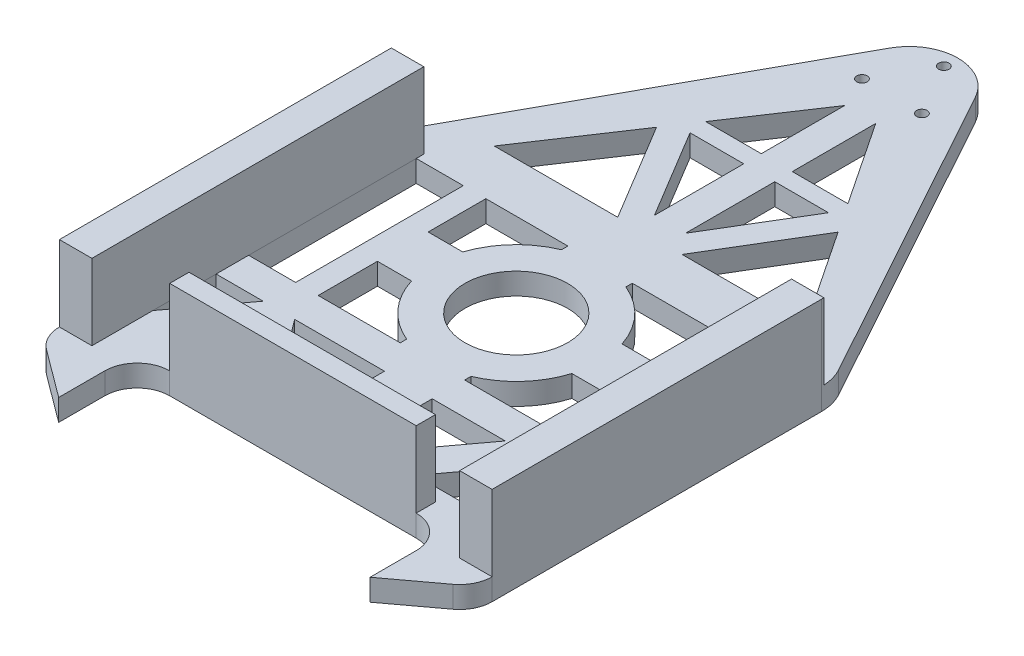
SolidWorks part; units mm, degrees
material "Cast Stainless Steel"
ref_plane "Front Plane" through (0, 0, 0) normal (0, 0, 1) x (1, 0, 0)
ref_plane "Top Plane" through (0, 0, 0) normal (0, 1, 0) x (1, 0, 0)
ref_plane "Right Plane" through (0, 0, 0) normal (1, 0, 0) x (0, 0, -1)
sketch "Sketch1" plane through (0, 0, 0) normal (0, 1, 0) x (1, 0, 0)
  line L0 (-324.5, 0) -> (-36.6111, 0)
  line L1 (19.4444, 0) -> (19.4444, 300)
  line L2 (-150.7834, 18.3812) -> (-143.0581, 18.3812)
  line L3 (-150.7834, 98.9559) -> (-83.2032, 98.9559)
  line L4 (-380.5556, 300) -> (-380.5556, 0)
  line L5 (-380.5556, 0) -> (-380.5556, -30.9894)
  line L6 (19.4444, 300) -> (25, 294.4444)
  line L7 (-350.5556, 98.9559) -> (-307.0461, 98.9559)
  line L8 (-350.5556, 40.385) -> (-307.0461, 98.9559)
  line L9 (-218.053, 18.3812) -> (-277.9079, 98.9559)
  line L10 (-143.0581, 18.3812) -> (-83.2032, 98.9559)
  line L11 (-40.2128, 30) -> (-97.0554, 30)
  line L12 (-350.5556, 128.9559) -> (-307.0461, 128.9559)
  line L13 (-194.896, 524.4061) -> (-246.3088, 447.2869)
  line L14 (-36.6111, 330) -> (-96.6333, 420.0334)
  line L15 (-324.5, 330) -> (-210.3278, 330)
  line L16 (-10.5556, 40.385) -> (-54.065, 98.9559)
  line L17 (-194.896, 18.3812) -> (-194.896, 98.9559)
  line L19 (-350.5556, 283.9559) -> (-307.0461, 283.9559)
  line L20 (-350.5556, 283.9559) -> (-350.5556, 221.4578)
  line L21 (-10.5556, 128.9559) -> (-10.5556, 178.791)
  line L22 (-350.5556, 300) -> (-350.5556, 0) construction
  line L23 (-380.5556, -30.9894) -> (-324.5, -72.6302)
  line L24 (-380.5556, 128.9559) -> (19.4444, 128.9559) construction
  line L25 (-292.477, 115.7535) -> (-292.477, 91.7007) construction
  line L26 (-97.0554, 30) -> (-68.6341, 68.2598)
  line L27 (-218.053, 18.3812) -> (-194.896, 18.3812)
  line L28 (-40.2128, 30) -> (-68.6341, 68.2598)
  line L29 (-320.8984, 30) -> (-264.0557, 30)
  line L30 (-150.7834, 330) -> (-36.6111, 330)
  line L31 (-320.8984, 30) -> (-292.477, 68.2598)
  line L32 (-54.065, 98.9559) -> (-10.5556, 98.9559)
  line L33 (-277.9079, 98.9559) -> (-194.896, 98.9559)
  line L34 (-264.0557, 30) -> (-292.477, 68.2598)
  line L35 (-380.5556, 98.9559) -> (19.4444, 98.9559) construction
  line L36 (-324.5, -72.6302) -> (-324.5, 0)
  line L37 (-36.6111, -72.6302) -> (-36.6111, 0)
  line L38 (-246.3088, 447.2869) -> (-194.896, 447.2869)
  line L39 (-180.5556, 424.8555) -> (-180.5556, 662.9762) construction
  line L40 (-380.5556, 300) -> (-180.5556, 662.9762)
  line L41 (-180.5556, 424.8555) -> (-180.5556, 353.486) construction
  line L42 (-180.5556, 662.9762) -> (19.4444, 300)
  line L43 (-150.7834, 18.3812) -> (-150.7834, 98.9559)
  line L44 (-307.0461, 283.9559) -> (-307.0461, 221.4578)
  line L45 (-286.1825, 283.9559) -> (-286.1825, 230.6106)
  line L46 (-548.4441, 206.4559) -> (-478.3267, 206.4559) construction
  line L47 (-307.0461, 128.9559) -> (-307.0461, 178.791)
  line L48 (-286.1825, 128.9559) -> (-286.1825, 183.7221)
  line L49 (19.4444, -30.9894) -> (-36.6111, -72.6302)
  line L50 (19.4444, 0) -> (19.4444, -30.9894)
  line L51 (-380.5556, 0) -> (-380.5556, -30.9894)
  line L52 (19.4444, 0) -> (19.4444, -30.9894)
  line L53 (-350.5556, 98.9559) -> (-350.5556, 40.385)
  line L54 (-10.5556, 98.9559) -> (-10.5556, 40.385)
  line L55 (-210.3278, 134.9027) -> (-210.3278, 128.9559)
  line L56 (-150.7834, 134.9027) -> (-150.7834, 128.9559)
  line L57 (-210.3278, 278.0092) -> (-210.3278, 283.9559)
  line L58 (-150.7834, 278.0092) -> (-150.7834, 283.9559)
  line L59 (-74.9286, 128.9559) -> (-74.9286, 183.7221)
  line L60 (-54.065, 128.9559) -> (-54.065, 178.791)
  line L61 (-74.9286, 283.9559) -> (-74.9286, 230.6106)
  line L62 (-54.065, 283.9559) -> (-54.065, 221.4578)
  line L63 (-350.5556, 178.791) -> (-350.5556, 128.9559)
  line L64 (-116.5717, 431.0826) -> (-166.2152, 431.0826)
  line L65 (-114.8023, 447.2869) -> (-166.2152, 524.4061)
  line L66 (-194.896, 524.4061) -> (-194.896, 447.2869)
  line L67 (-166.2152, 524.4061) -> (-166.2152, 447.2869)
  line L68 (-244.5394, 431.0826) -> (-194.896, 348.542)
  line L69 (-264.4778, 420.0334) -> (-210.3278, 330)
  line L70 (-116.5717, 431.0826) -> (-166.2152, 348.542)
  line L71 (-96.6333, 420.0334) -> (-150.7834, 330)
  line L72 (-166.2152, 447.2869) -> (-114.8023, 447.2869)
  line L73 (-194.896, 431.0826) -> (-244.5394, 431.0826)
  line L74 (-194.896, 431.0826) -> (-194.896, 348.542)
  line L75 (-166.2152, 431.0826) -> (-166.2152, 348.542)
  line L76 (-264.4778, 420.0334) -> (-324.5, 330)
  line L77 (-10.5556, 221.4578) -> (-10.5556, 283.9559)
  line L78 (-74.9286, 183.7221) -> (-106.4649, 183.7221)
  line L79 (-74.9286, 230.6106) -> (-106.9159, 230.6106)
  line L80 (-286.1825, 183.7221) -> (-254.6462, 183.7221)
  line L81 (-286.1825, 230.6106) -> (-254.1952, 230.6106)
  line L82 (-286.1825, 283.9559) -> (-210.3278, 283.9559)
  line L83 (-286.1825, 128.9559) -> (-210.3278, 128.9559)
  line L84 (-54.065, 128.9559) -> (-10.5556, 128.9559)
  line L85 (-54.065, 283.9559) -> (-10.5556, 283.9559)
  line L86 (-150.7834, 283.9559) -> (-74.9286, 283.9559)
  line L87 (-150.7834, 128.9559) -> (-74.9286, 128.9559)
  line L88 (-10.5556, 221.4578) -> (-10.5556, 178.791)
  line L89 (-54.065, 221.4578) -> (-54.065, 178.791)
  line L90 (-307.0461, 221.4578) -> (-307.0461, 178.791)
  line L91 (-350.5556, 221.4578) -> (-350.5556, 178.791)
  arc A0 (-254.6462, 183.7221) -> (-210.3278, 134.9027) centre (-180.5556, 206.4559) ccw
  circle A1 centre (-180.5556, 206.4559) radius 47.5
  arc A2 (-106.9159, 230.6106) -> (-150.7834, 278.0092) centre (-180.5556, 206.4559) ccw
  circle A3 centre (-180.5556, 206.4559) radius 77.5 construction
  arc A4 (-210.3278, 278.0092) -> (-254.1952, 230.6106) centre (-180.5556, 206.4559) ccw
  arc A5 (-150.7834, 134.9027) -> (-106.4649, 183.7221) centre (-180.5556, 206.4559) ccw
  point P3 (-180.5556, 0)
  point P11 (-279.5115, 98.9559)
  point P12 (-5.5171, 283.359)
  point P13 (-81.5996, 98.9559)
  point P14 (-180.5556, 545.9167)
  point P15 (-355.594, 283.359)
  point P16 (-380.5556, 330)
  point P17 (19.4444, 330)
  point P23 (-10.5556, 0)
  point P24 (-10.5556, 300)
  point P25 (-380.5556, 270)
  point P26 (19.4444, 270)
  point P33 (-81.3793, 56.7498)
  point P34 (-1.5461, -21.4335)
  point P35 (-180.5556, -42.4264)
  point P36 (-279.7318, 56.7498)
  point P37 (-359.565, -21.4335)
  point P38 (-380.5556, 30)
  point P39 (19.4444, 30)
  point P69 (-307.0461, 153.8735)
  point P74 (-356.4732, -17.8896)
  point P83 (-54.065, 153.8735)
  point P93 (-113.115, 220.0966)
  point P112 (-282.9637, 81.0663)
  point P113 (-228.4809, -17.8896)
  point P114 (-301.9903, 81.0663)
  point P115 (-380.5556, 30)
  point P126 (-328.8008, 128.9559)
  dimension "D1" = 155
  dimension "D3" = 400
  dimension "D8" = 53.393
  dimension "D5" = 30
  dimension "D7" = 30
  dimension "D9" = 30
extrude "Boss-Extrude6" add sketch "Sketch1" along normal blind 20
fillet "Fillet2" radius 30 4 edges at (-324.5, 10, 0) (-36.6111, 10, 0) (19.4444, 10, 30.9894) (-380.5556, 10, 30.9894)
sketch "Sketch3" plane through (0, 20, 0) normal (0, 1, 0) x (1, 0, 0)
  line L0 (-294.5, 0) -> (-66.6111, 0)
  line L1 (-294.5, 0) -> (-294.5, 17.8282)
  line L2 (-66.6111, 0) -> (-66.6111, 17.8282)
  line L3 (-294.5, 17.8282) -> (-66.6111, 17.8282)
  line L4 (-380.5556, -15.9032) -> (-380.5556, 290.9167)
  line L5 (-380.5556, -15.9032) -> (-350.5259, -15.9032)
  line L6 (-380.5556, 290.9167) -> (-350.5259, 290.9167)
  line L7 (-350.5259, -15.9032) -> (-350.5259, 290.9167)
  line L8 (19.4444, -15.9032) -> (19.4444, 290.9167)
  line L9 (19.4444, -15.9032) -> (-10.5556, -15.9032)
  line L10 (19.4444, 290.9167) -> (-10.5556, 290.9167)
  line L11 (-10.5556, -15.9032) -> (-10.5556, 290.9167)
extrude "Boss-Extrude12" add sketch "Sketch3" along normal blind 70
fillet "Fillet3" radius 45 1 edges at (-180.5556, 10, -662.9762)
fillet "Fillet4" radius 45 2 edges at (-380.5556, 10, -300) (19.4444, 10, -300)
sketch "Sketch4" plane through (0, 20, 0) normal (0, 1, 0) x (1, 0, 0)
  line L0 (-180.5556, 569.7296) -> (-180.5556, 601.7296) construction
  line L1 (-180.5556, 601.7296) -> (-180.5556, 569.7296) construction
  line L2 (-208.2684, 553.7296) -> (-180.5556, 569.7296) construction
  line L3 (-180.5556, 569.7296) -> (-152.8427, 553.7296) construction
  circle A2 centre (-180.5556, 601.7296) radius 4.8525
  circle A3 centre (-208.2684, 553.7296) radius 4.8525
  circle A4 centre (-152.8427, 553.7296) radius 4.8525
  dimension "D1" = 120
  dimension "D2" = 120
  dimension "D3" = 32
  dimension "D4" = 32
  dimension "D5" = 32
extrude "Cut-Extrude2" cut sketch "Sketch4" against normal through all
